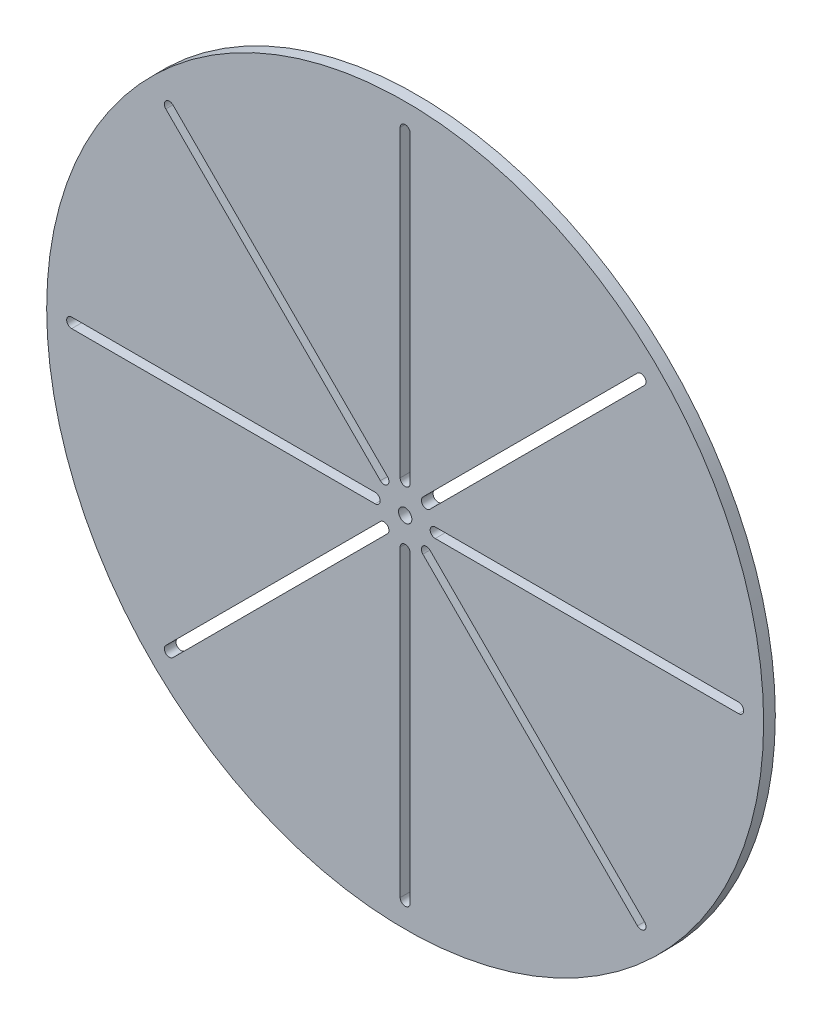
SolidWorks part; units mm, degrees
ref_plane "Front Plane" through (0, 0, 0) normal (0, 0, 1) x (1, 0, 0)
ref_plane "Top Plane" through (0, 0, 0) normal (0, 1, 0) x (1, 0, 0)
ref_plane "Right Plane" through (0, 0, 0) normal (1, 0, 0) x (0, 0, -1)
sketch "Sketch1" plane through (0, 0, 0) normal (0, 0, 1) x (1, 0, 0)
  line L0 (0, 0) -> (100, 0) construction
  line L1 (9, 0) -> (100, 0) construction
  line L2 (9, 1.5) -> (100, 1.5)
  line L3 (9, -1.5) -> (100, -1.5)
  line L4 (6.364, -6.364) -> (70.7107, -70.7107) construction
  line L5 (7.4246, -5.3033) -> (71.7713, -69.65)
  line L6 (5.3033, -7.4246) -> (69.65, -71.7713)
  line L7 (0, -9) -> (0, -100) construction
  line L8 (1.5, -9) -> (1.5, -100)
  line L9 (-1.5, -9) -> (-1.5, -100)
  line L10 (-6.364, -6.364) -> (-70.7107, -70.7107) construction
  line L11 (-5.3033, -7.4246) -> (-69.65, -71.7713)
  line L12 (-7.4246, -5.3033) -> (-71.7713, -69.65)
  line L13 (-9, 0) -> (-100, 0) construction
  line L14 (-9, -1.5) -> (-100, -1.5)
  line L15 (-9, 1.5) -> (-100, 1.5)
  line L16 (-6.364, 6.364) -> (-70.7107, 70.7107) construction
  line L17 (-7.4246, 5.3033) -> (-71.7713, 69.65)
  line L18 (-5.3033, 7.4246) -> (-69.65, 71.7713)
  line L19 (0, 9) -> (0, 100) construction
  line L20 (-1.5, 9) -> (-1.5, 100)
  line L21 (1.5, 9) -> (1.5, 100)
  line L22 (6.364, 6.364) -> (70.7107, 70.7107) construction
  line L23 (5.3033, 7.4246) -> (69.65, 71.7713)
  line L24 (7.4246, 5.3033) -> (71.7713, 69.65)
  line L25 (100, 0) -> (105, 0) construction
  line L26 (0, 0) -> (50.905, 91.8351) construction
  circle A0 centre (0, 0) radius 107.5
  circle A1 centre (0, 0) radius 105 construction
  circle A2 centre (0, 0) radius 9 construction
  circle A3 centre (0, 0) radius 2
  circle A4 centre (0, 0) radius 100 construction
  arc A5 (9, 1.5) -> (9, -1.5) centre (9, 0) ccw
  arc A6 (100, -1.5) -> (100, 1.5) centre (100, 0) ccw
  arc A7 (7.4246, -5.3033) -> (5.3033, -7.4246) centre (6.364, -6.364) ccw
  arc A8 (69.65, -71.7713) -> (71.7713, -69.65) centre (70.7107, -70.7107) ccw
  arc A9 (1.5, -9) -> (-1.5, -9) centre (0, -9) ccw
  arc A10 (-1.5, -100) -> (1.5, -100) centre (0, -100) ccw
  arc A11 (-5.3033, -7.4246) -> (-7.4246, -5.3033) centre (-6.364, -6.364) ccw
  arc A12 (-71.7713, -69.65) -> (-69.65, -71.7713) centre (-70.7107, -70.7107) ccw
  arc A13 (-9, -1.5) -> (-9, 1.5) centre (-9, 0) ccw
  arc A14 (-100, 1.5) -> (-100, -1.5) centre (-100, 0) ccw
  arc A15 (-7.4246, 5.3033) -> (-5.3033, 7.4246) centre (-6.364, 6.364) ccw
  arc A16 (-69.65, 71.7713) -> (-71.7713, 69.65) centre (-70.7107, 70.7107) ccw
  arc A17 (-1.5, 9) -> (1.5, 9) centre (0, 9) ccw
  arc A18 (1.5, 100) -> (-1.5, 100) centre (0, 100) ccw
  arc A19 (5.3033, 7.4246) -> (7.4246, 5.3033) centre (6.364, 6.364) ccw
  arc A20 (71.7713, 69.65) -> (69.65, 71.7713) centre (70.7107, 70.7107) ccw
  point P9 (54.5, 0)
  point P18 (38.5373, -38.5373)
  point P25 (0, -54.5)
  point P32 (-38.5373, -38.5373)
  point P39 (-54.5, 0)
  point P46 (-38.5373, 38.5373)
  point P53 (0, 54.5)
  point P60 (38.5373, 38.5373)
  point P65 (0, 0)
  point P84 (0, 0)
  dimension "D1" = 215
  dimension "D2" = 2.5
  dimension "D3" = 18
  dimension "D4" = 4
  dimension "D5" = 200
  dimension "D8" = 61
  dimension "D6" = 3
  dimension "D7" = 8
extrude "Boss-Extrude1" add sketch "Sketch1" along normal blind 3.5
